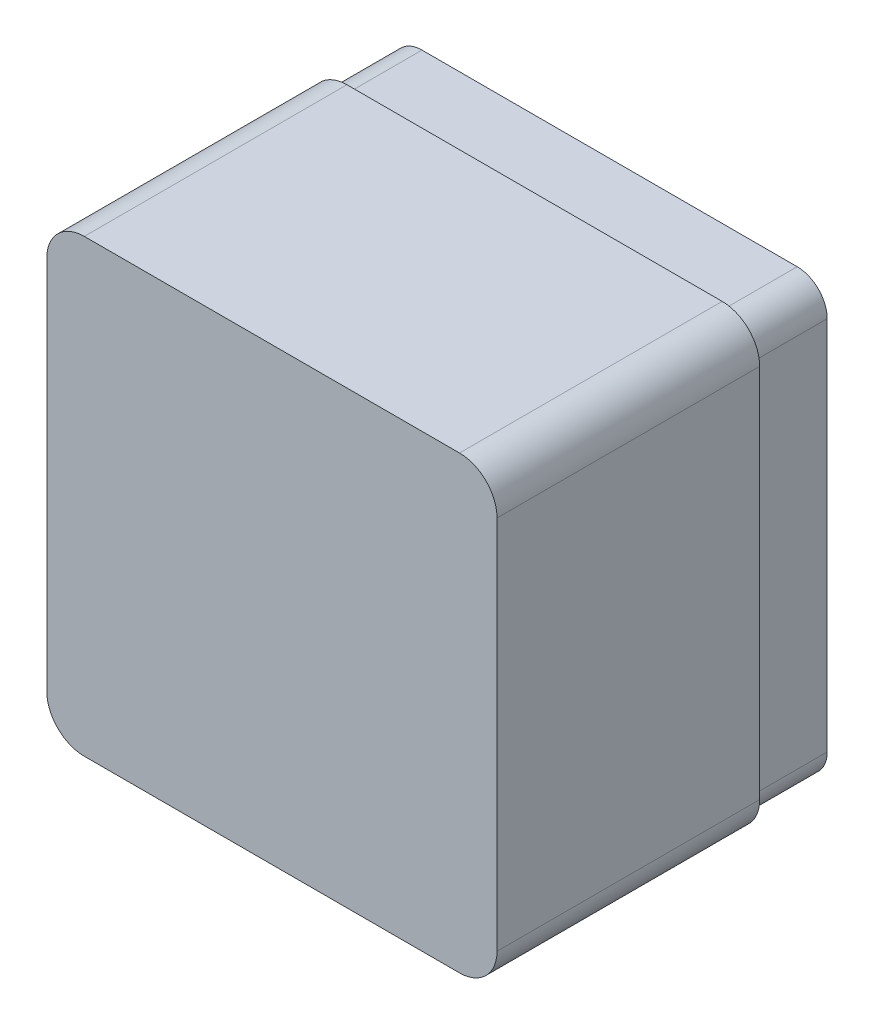
SolidWorks part; units mm, degrees
ref_plane "Front Plane" through (0, 0, 0) normal (0, 0, 1) x (1, 0, 0)
ref_plane "Top Plane" through (0, 0, 0) normal (0, 1, 0) x (1, 0, 0)
ref_plane "Right Plane" through (0, 0, 0) normal (1, 0, 0) x (0, 0, -1)
sketch "Sketch2" plane through (0, 0, 0) normal (0, 0, 1) x (1, 0, 0)
  line L1 (0, 0) -> (120, 0)
  line L2 (0, 0) -> (0, 120)
  line L3 (0, 120) -> (120, 120)
  line L4 (120, 0) -> (120, 120)
  dimension "D1" = 120
  dimension "D2" = 120
extrude "Boss-Extrude1" add sketch "Sketch2" along normal blind 90
fillet "Fillet1" radius 10 4 edges at (0, 0, 45) (120, 0, 45) (120, 120, 45) (0, 120, 45)
shell "Shell2" thickness 4
sketch "Sketch4" plane through (0, 0, 0) normal (0, 0, -1) x (-1, 0, 0)
  line L12 (-110, 2) -> (-10, 2)
  line L13 (-2, 10) -> (-2, 110)
  line L14 (-10, 118) -> (-110, 118)
  line L15 (-118, 110) -> (-118, 10)
  line L16 (-110, 2) -> (-10, 2)
  line L17 (-2, 10) -> (-2, 110)
  line L18 (-10, 118) -> (-110, 118)
  line L19 (-118, 110) -> (-118, 10)
  arc A12 (-10, 2) -> (-2, 10) centre (-10, 10) ccw
  arc A13 (-2, 110) -> (-10, 118) centre (-10, 110) ccw
  arc A14 (-110, 118) -> (-118, 110) centre (-110, 110) ccw
  arc A15 (-118, 10) -> (-110, 2) centre (-110, 10) ccw
  arc A16 (-10, 2) -> (-2, 10) centre (-10, 10) ccw
  arc A17 (-2, 110) -> (-10, 118) centre (-10, 110) ccw
  arc A18 (-110, 118) -> (-118, 110) centre (-110, 110) ccw
  arc A19 (-118, 10) -> (-110, 2) centre (-110, 10) ccw
  dimension "D1" = 2
extrude "Cut-Extrude5" cut sketch "Sketch4" against normal blind 20 flip side to cut contours L18 A18 L19 A19 L16 A16 L17 A17
